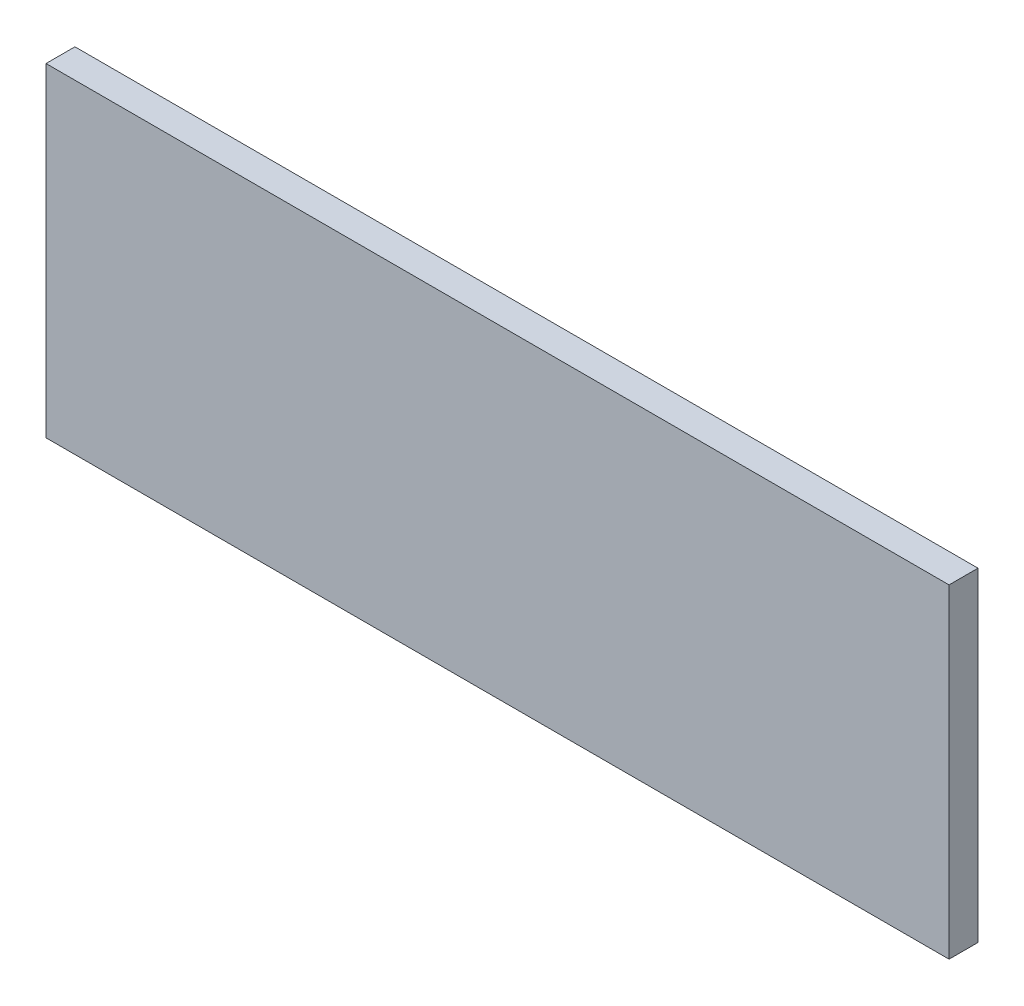
SolidWorks part; units mm, degrees
ref_plane "Front Plane" through (0, 0, 0) normal (0, 0, 1) x (1, 0, 0)
ref_plane "Top Plane" through (0, 0, 0) normal (0, 1, 0) x (1, 0, 0)
ref_plane "Right Plane" through (0, 0, 0) normal (1, 0, 0) x (0, 0, -1)
sketch "Sketch1" plane through (0, 0, 0) normal (0, 0, 1) x (1, 0, 0)
  line L0 (-36.115, 16.9218) -> (41.885, 16.9218)
  line L1 (41.885, 16.9218) -> (41.885, -11.0782)
  line L2 (41.885, -11.0782) -> (-36.115, -11.0782)
  line L3 (-36.115, 16.9218) -> (-36.115, -11.0782)
  dimension "D1" = 78
  dimension "D2" = 28
extrude "Boss-Extrude1" add sketch "Sketch1" along normal blind 2.5
